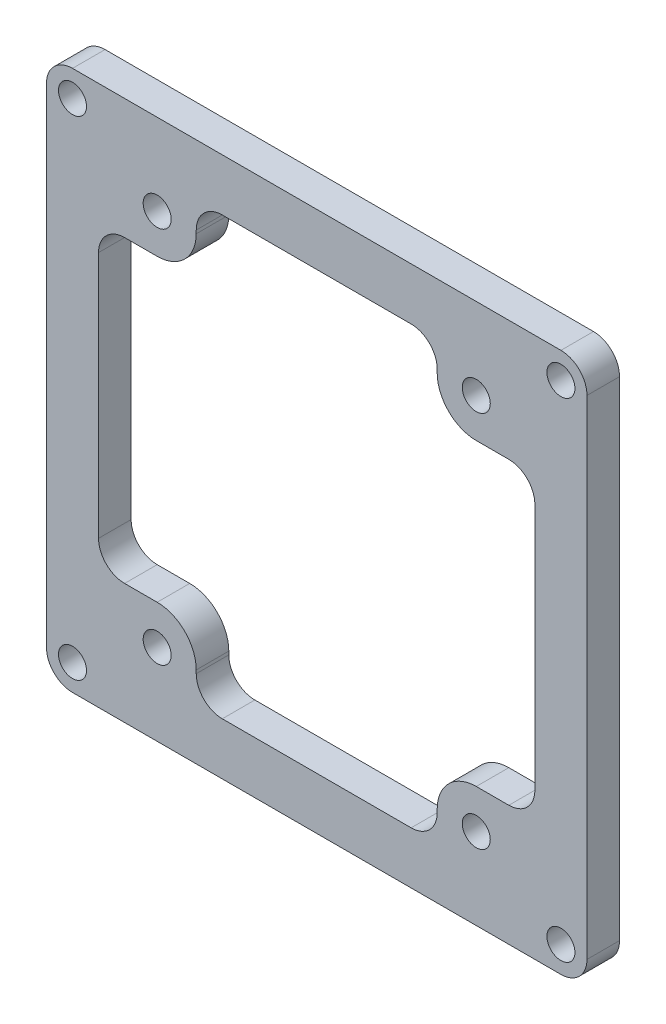
SolidWorks part; units mm, degrees
material "ABS"
ref_plane "Plan de face" through (0, 0, 0) normal (0, 0, 1) x (1, 0, 0)
ref_plane "Plan de dessus" through (0, 0, 0) normal (0, 1, 0) x (1, 0, 0)
ref_plane "Plan de droite" through (0, 0, 0) normal (1, 0, 0) x (0, 0, -1)
sketch "Esquisse1" plane through (0, 0, 0) normal (0, 0, 1) x (1, 0, 0)
  line L0 (-14.5, -33.5) -> (14.5, -33.5)
  line L1 (-37.5, -37.5) -> (37.5, -37.5) construction
  line L2 (-37.5, -37.5) -> (-37.5, 37.5) construction
  line L3 (-37.5, 37.5) -> (37.5, 37.5) construction
  line L4 (37.5, -37.5) -> (37.5, 37.5) construction
  line L5 (-37.5, -37.5) -> (37.5, 37.5) construction
  line L6 (-37.5, 37.5) -> (37.5, -37.5) construction
  line L7 (33.5, -19) -> (33.5, 19)
  line L8 (-14.5, 33.5) -> (14.5, 33.5)
  line L9 (-33.5, -19) -> (-33.5, 19)
  line L10 (-37.5, -41.5) -> (37.5, -41.5)
  line L11 (41.5, -37.5) -> (41.5, 37.5)
  line L12 (-37.5, 41.5) -> (37.5, 41.5)
  line L13 (-41.5, -37.5) -> (-41.5, 37.5)
  line L14 (-41.5, -41.5) -> (41.5, -41.5) construction
  line L15 (-41.5, -41.5) -> (-41.5, 41.5) construction
  line L16 (41.5, -41.5) -> (41.5, 41.5) construction
  line L17 (-41.5, 41.5) -> (41.5, 41.5) construction
  line L19 (-24.5, -29) -> (24.5, -29) construction
  line L20 (-24.5, -29) -> (-24.5, 29) construction
  line L21 (-24.5, 29) -> (24.5, 29) construction
  line L22 (24.5, -29) -> (24.5, 29) construction
  line L23 (-24.5, -29) -> (24.5, 29) construction
  line L24 (-24.5, 29) -> (24.5, -29) construction
  line L28 (-24.5, 23) -> (-29.5, 23)
  line L29 (-18.5, 29) -> (-18.5, 29.5)
  line L30 (18.5, 29) -> (18.5, 29.5)
  line L31 (24.5, 23) -> (29.5, 23)
  line L32 (24.5, -23) -> (29.5, -23)
  line L33 (18.5, -29) -> (18.5, -29.5)
  line L34 (-24.5, -23) -> (-29.5, -23)
  line L35 (-18.5, -29) -> (-18.5, -29.5)
  line L37 (-33.5, -33.5) -> (-33.5, 33.5) construction
  line L38 (-33.5, 33.5) -> (33.5, 33.5) construction
  line L39 (33.5, -33.5) -> (33.5, 33.5) construction
  line L40 (-33.5, -33.5) -> (33.5, -33.5) construction
  arc A0 (-37.5, -41.5) -> (-41.5, -37.5) centre (-37.5, -37.5) cw
  arc A1 (37.5, -41.5) -> (41.5, -37.5) centre (37.5, -37.5) ccw
  arc A2 (41.5, 37.5) -> (37.5, 41.5) centre (37.5, 37.5) ccw
  arc A3 (-37.5, 41.5) -> (-41.5, 37.5) centre (-37.5, 37.5) ccw
  arc A4 (-24.5, 23) -> (-18.5, 29) centre (-24.5, 29) ccw
  arc A5 (18.5, 29) -> (24.5, 23) centre (24.5, 29) ccw
  arc A6 (24.5, -23) -> (18.5, -29) centre (24.5, -29) ccw
  arc A7 (-18.5, -29) -> (-24.5, -23) centre (-24.5, -29) ccw
  arc A8 (18.5, 29.5) -> (14.5, 33.5) centre (14.5, 29.5) ccw
  arc A9 (29.5, 23) -> (33.5, 19) centre (29.5, 19) cw
  arc A10 (29.5, -23) -> (33.5, -19) centre (29.5, -19) ccw
  arc A11 (18.5, -29.5) -> (14.5, -33.5) centre (14.5, -29.5) cw
  arc A12 (-18.5, -29.5) -> (-14.5, -33.5) centre (-14.5, -29.5) ccw
  arc A13 (-29.5, -23) -> (-33.5, -19) centre (-29.5, -19) cw
  arc A14 (-29.5, 23) -> (-33.5, 19) centre (-29.5, 19) ccw
  arc A15 (-18.5, 29.5) -> (-14.5, 33.5) centre (-14.5, 29.5) cw
  point P0 (0, 0)
  point P26 (0, 0)
  dimension "D5" = 4
  dimension "D8" = 12
  dimension "D9" = 4
  dimension "D1" = 75
  dimension "D2" = 75
  dimension "D6" = 49
  dimension "D7" = 58
  dimension "D3" = 4
  dimension "D4" = 4
extrude "Boss.-Extru.1" add sketch "Esquisse1" along normal blind 5
hole_wizard "Dégagement M41" positions "Esquisse2" profile "Esquisse3" hole size "M4" standard "ISO"
sketch "Esquisse2" plane through (0, 0, 5) normal (0, 0, 1) x (1, 0, 0)
  point P0 (-37.5, 37.5)
  point P3 (37.5, 37.5)
  point P6 (37.5, -37.5)
  point P9 (-37.5, -37.5)
  point P13 (-24.5, 29)
  point P16 (24.5, 29)
  point P19 (24.5, -29)
  point P22 (-24.5, -29)
sketch "Esquisse3" plane through (-37.5, 37.5, 5) normal (1, 0, 0) x (0, -1, 0)
  line L0 (0, 0) -> (0, 11.2919)
  line L1 (0, 11.2919) -> (2.15, 10)
  line L2 (2.15, 10) -> (2.15, 0)
  line L5 (2.15, 0) -> (0, 0)
  line L10 (0, 11.2919) -> (-2.15, 10) construction
  line L11 (0, -6.35) -> (0, 107.95) construction
  dimension "Diamètre du perçage" = 4.3
  dimension "Profondeur du perçage" = 10
  dimension "Angle de pointe" = 118
